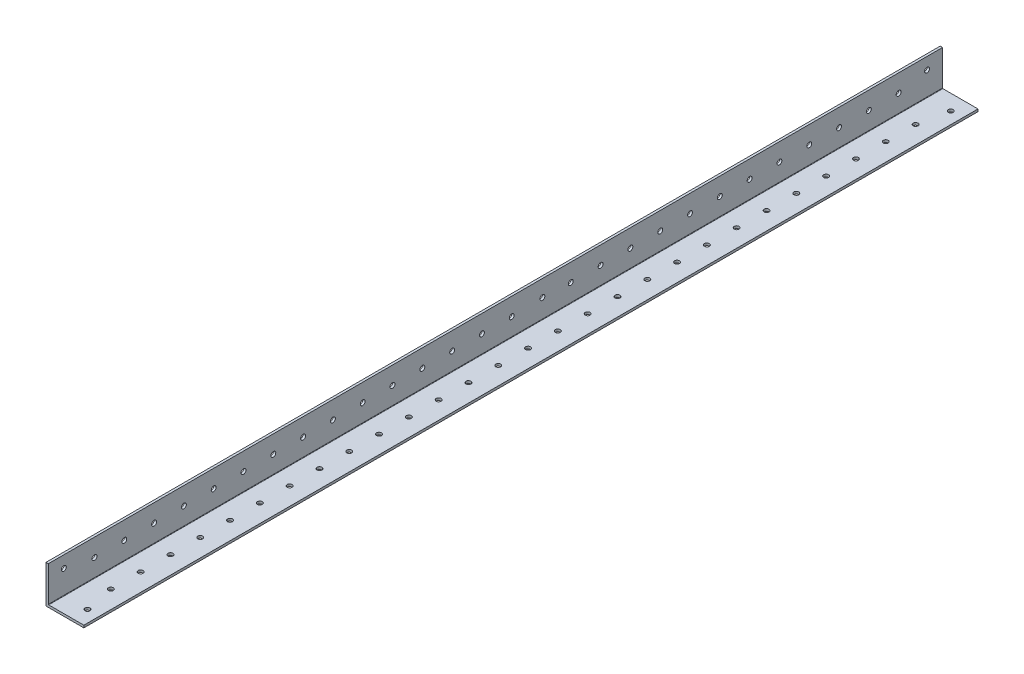
SolidWorks part; units mm, degrees
ref_plane "Front Plane" through (0, 0, 0) normal (0, 0, 1) x (1, 0, 0)
ref_plane "Top Plane" through (0, 0, 0) normal (0, 1, 0) x (1, 0, 0)
ref_plane "Right Plane" through (0, 0, 0) normal (1, 0, 0) x (0, 0, -1)
sketch "Sketch1" plane through (0, 0, 0) normal (0, 0, 1) x (1, 0, 0)
  line L0 (0, 25.4) -> (0, 0) construction
  line L1 (0, 0) -> (25.4, 0) construction
  line L2 (25.4, 0) -> (25.4, 1.5875) construction
  line L3 (25.4, 1.5875) -> (1.5875, 1.5875) construction
  line L4 (1.5875, 1.5875) -> (1.5875, 25.4) construction
  line L6 (1.5875, 25.4) -> (0, 25.4) construction
  arc A0 (1.5875, 1.8415) -> (1.8415, 1.5875) centre (1.8415, 1.8415) ccw construction
  point P4 (0, 0)
  dimension "Inside Corner Radius" = 0.254
  dimension "Outside Height" = 25.4
  dimension "Inside Height" = 23.8125
  dimension "Outside Width" = 25.4
  dimension "Inside Width" = 23.8125
  dimension "Wall Thickness" = 1.5875
  dimension "Shape" = 90
sketch "Sketch2" plane through (0, 0, 0) normal (1, 0, 0) x (0, 0, -1)
  line L0 (1219.2, 0) -> (-1219.2, 0) construction
  line L1 (-1219.2, 25.4) -> (-1219.2, 0) construction
  line L2 (1219.2, 25.4) -> (1219.2, 0) construction
  point P0 (-1189.99, 0)
  point P4 (0, 0)
  point P6 (1189.99, 0)
  dimension "D1" = 29.21
  dimension "D2" = 29.21
  dimension "D3" = 25.4
  dimension "Length" = 2438.4
sketch "Sketch3" plane through (0, 0, 0) normal (0, 0, 1) x (1, 0, 0)
  line L0 (1.5875, 25.4) -> (0, 25.4)
  line L1 (0, 25.4) -> (0, 0)
  line L2 (0, 0) -> (25.4, 0)
  line L3 (25.4, 0) -> (25.4, 1.5875)
  line L4 (25.4, 1.5875) -> (1.5875, 1.5875)
  line L5 (1.5875, 1.5875) -> (1.5875, 25.4)
extrude "Boss-Extrude1" add sketch "Sketch3" along normal mid plane 2438.4
fillet "Fillet1" radius 0.254 1 edges at (1.5875, 1.5875, 0)
sketch "Sketch4" plane through (0, 0, 0) normal (-1, 0, 0) x (0, 0, 1)
  line L0 (1219.2, 25.4) -> (1219.2, 0) construction
  line L1 (-1219.2, 0) -> (619.2, 0)
  line L2 (-1219.2, 0) -> (-1219.2, 74.9453)
  line L3 (-1219.2, 74.9453) -> (619.2, 74.9453)
  line L4 (619.2, 0) -> (619.2, 74.9453)
  dimension "D1" = 600
extrude "Cut-Extrude1" cut sketch "Sketch4" against normal blind 60
sketch "Sketch5" plane through (0, 1.5875, 0) normal (0, 1, 0) x (1, 0, 0)
  line L0 (17.4625, -1208.8241) -> (17.4625, -1189.2) construction
  line L1 (13.4937, -649.2) -> (13.4937, -629.5759) construction
  line L3 (1.5875, -1189.2) -> (25.4, -1189.2) construction
  line L4 (1.5875, -1219.2) -> (1.5875, -619.2) construction
  line L5 (25.4, -1219.2) -> (25.4, -619.2) construction
  line L6 (13.4937, -629.5759) -> (17.4625, -629.5759) construction
  line L7 (17.4625, -629.5759) -> (13.4937, -629.5759) construction
  circle A30 centre (17.4625, -629.5759) radius 1.65
  circle A31 centre (17.4625, -1208.8241) radius 1.65
  circle A32 centre (13.4938, -1189.2) radius 1.65
  circle A33 centre (13.4938, -1169.2) radius 1.65
  circle A34 centre (13.4938, -1149.2) radius 1.65
  circle A35 centre (13.4938, -1129.2) radius 1.65
  circle A36 centre (13.4938, -1109.2) radius 1.65
  circle A37 centre (13.4938, -1089.2) radius 1.65
  circle A38 centre (13.4938, -1069.2) radius 1.65
  circle A39 centre (13.4938, -1049.2) radius 1.65
  circle A40 centre (13.4938, -1029.2) radius 1.65
  circle A41 centre (13.4938, -1009.2) radius 1.65
  circle A42 centre (13.4938, -989.2) radius 1.65
  circle A43 centre (13.4938, -969.2) radius 1.65
  circle A44 centre (13.4938, -949.2) radius 1.65
  circle A45 centre (13.4938, -929.2) radius 1.65
  circle A46 centre (13.4938, -909.2) radius 1.65
  circle A47 centre (13.4938, -889.2) radius 1.65
  circle A48 centre (13.4938, -869.2) radius 1.65
  circle A49 centre (13.4938, -849.2) radius 1.65
  circle A50 centre (13.4938, -829.2) radius 1.65
  circle A51 centre (13.4938, -809.2) radius 1.65
  circle A52 centre (13.4938, -789.2) radius 1.65
  circle A53 centre (13.4938, -769.2) radius 1.65
  circle A54 centre (13.4938, -749.2) radius 1.65
  circle A55 centre (13.4938, -729.2) radius 1.65
  circle A56 centre (13.4938, -709.2) radius 1.65
  circle A57 centre (13.4938, -689.2) radius 1.65
  circle A58 centre (13.4938, -669.2) radius 1.65
  circle A59 centre (13.4937, -649.2) radius 1.65
  point P9 (0, 0)
  dimension "D1" = 3.3
  dimension "D2" = 3.3
  dimension "D3" = 28
  dimension "D4" = 20
extrude "Cut-Extrude2" cut sketch "Sketch5" against normal blind 10
sketch "Sketch9" plane through (1.5875, 0, 0) normal (1, 0, 0) x (0, 0, -1)
  line L0 (-648.6348, 1.5875) -> (-648.6348, 25.4) construction
  line L1 (-1219.2, 1.5875) -> (-619.2, 1.5875) construction
  line L2 (-1219.2, 25.4) -> (-619.2, 25.4) construction
  line L3 (-629.5759, 17.4625) -> (-648.6348, 17.4625) construction
  line L4 (-634.3937, -3.175) -> (-630.9937, -3.175) construction
  line L5 (-634.3937, 0) -> (-634.3937, -6.35) construction
  line L6 (-630.9937, -6.35) -> (-630.9937, 0) construction
  line L7 (-632.6937, -3.175) -> (-887.6937, -3.175) construction
  line L8 (-887.6937, -3.175) -> (-887.6937, 25.4) construction
  line L9 (-868.6348, 13.4937) -> (-887.6937, 13.4937) construction
  line L10 (-908.2589, 1.5875) -> (-908.2589, 25.4) construction
  line L11 (-908.2589, 10.4618) -> (-887.6937, 10.4618) construction
  line L12 (-1208.8241, 17.4625) -> (-1208.8241, 3.8186) construction
  line L13 (-1215.3265, 3.8186) -> (-1204.9125, 3.8186) construction
  line L14 (-1188.2589, 13.4937) -> (-1208.8241, 13.4937) construction
  circle A0 centre (-629.5759, 17.4625) radius 1.65
  circle A1 centre (-648.6348, 13.4938) radius 1.65
  circle A2 centre (-887.6937, 14.2875) radius 1.65
  circle A3 centre (-1208.8241, 17.4625) radius 1.65
  circle A4 centre (-668.6348, 13.4938) radius 1.65
  circle A5 centre (-688.6348, 13.4938) radius 1.65
  circle A6 centre (-708.6348, 13.4938) radius 1.65
  circle A7 centre (-728.6348, 13.4938) radius 1.65
  circle A8 centre (-748.6348, 13.4938) radius 1.65
  circle A9 centre (-768.6348, 13.4938) radius 1.65
  circle A10 centre (-788.6348, 13.4938) radius 1.65
  circle A11 centre (-808.6348, 13.4938) radius 1.65
  circle A12 centre (-828.6348, 13.4938) radius 1.65
  circle A13 centre (-848.6348, 13.4938) radius 1.65
  circle A14 centre (-868.6348, 13.4937) radius 1.65
  circle A16 centre (-888.6348, 13.4937) radius 1.65 [skipped]
  circle A17 centre (-908.2589, 13.4938) radius 1.65
  circle A18 centre (-928.2589, 13.4938) radius 1.65
  circle A19 centre (-948.2589, 13.4938) radius 1.65
  circle A20 centre (-968.2589, 13.4938) radius 1.65
  circle A21 centre (-988.2589, 13.4938) radius 1.65
  circle A22 centre (-1008.2589, 13.4938) radius 1.65
  circle A23 centre (-1028.2589, 13.4938) radius 1.65
  circle A24 centre (-1048.2589, 13.4938) radius 1.65
  circle A25 centre (-1068.2589, 13.4938) radius 1.65
  circle A26 centre (-1088.2589, 13.4938) radius 1.65
  circle A27 centre (-1108.2589, 13.4938) radius 1.65
  circle A28 centre (-1128.2589, 13.4938) radius 1.65
  circle A29 centre (-1148.2589, 13.4938) radius 1.65
  circle A30 centre (-1168.2589, 13.4938) radius 1.65
  circle A31 centre (-1188.2589, 13.4937) radius 1.65
  dimension "D1" = 12.7
  dimension "D3" = 3.3
  dimension "D2" = 255
  dimension "D5" = 20
  dimension "D6" = 20
  dimension "D4" = 13
extrude "Cut-Extrude6" cut sketch "Sketch9" against normal blind 60
equation "\"D1@Boss-Extrude1\"=\"Length@Sketch2\""
equation "\"D1@Sketch2\" = \"Outside Width@Sketch1\" * 1.15"
equation "\"D2@Sketch2\"=\"D1@Sketch2\""
equation "\"D1@Fillet1\"=\"Inside Corner Radius@Sketch1\""
equation "\"D3@Sketch2\"=\"Outside Height@Sketch1\""
